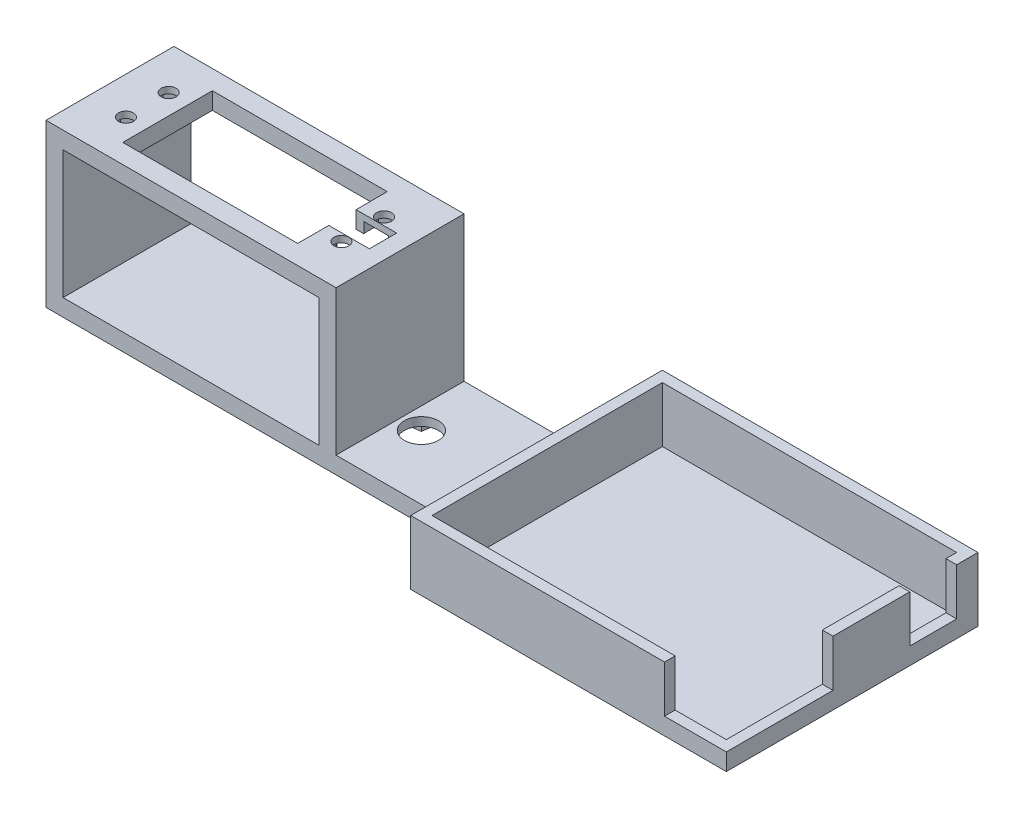
SolidWorks part; units mm, degrees
ref_plane "Front Plane" through (0, 0, 0) normal (0, 0, 1) x (1, 0, 0)
ref_plane "Top Plane" through (0, 0, 0) normal (0, 1, 0) x (1, 0, 0)
ref_plane "Right Plane" through (0, 0, 0) normal (1, 0, 0) x (0, 0, -1)
sketch "Sketch1" plane through (0, 0, 0) normal (0, 1, 0) x (1, 0, 0)
  line L1 (-37, -29.5) -> (37, -29.5)
  line L2 (-37, -29.5) -> (-37, 29.5)
  line L3 (-37, 29.5) -> (37, 29.5)
  line L4 (37, -29.5) -> (37, 29.5)
  line L5 (-37, -29.5) -> (37, 29.5) construction
  line L6 (-37, 29.5) -> (37, -29.5) construction
  point P0 (0, 0)
  dimension "D1" = 59
  dimension "D2" = 74
extrude "Boss-Extrude1" add sketch "Sketch1" along normal blind 2
sketch "Sketch2" plane through (0, 2, 0) normal (0, 1, 0) x (1, 0, 0)
  line L1 (-37, -29.5) -> (37, -29.5)
  line L2 (-37, -29.5) -> (-37, 29.5)
  line L3 (-37, 29.5) -> (37, 29.5)
  line L4 (37, -29.5) -> (37, 29.5)
  line L5 (-37, -29.5) -> (37, 29.5) construction
  line L6 (-37, 29.5) -> (37, -29.5) construction
  line L7 (-34.5, -27) -> (34.5, -27)
  line L8 (-34.5, -27) -> (-34.5, 27)
  line L9 (-34.5, 27) -> (34.5, 27)
  line L10 (34.5, -27) -> (34.5, 27)
  line L11 (-34.5, -27) -> (34.5, 27) construction
  line L12 (-34.5, 27) -> (34.5, -27) construction
  point P0 (0, 0)
  point P7 (0, 0)
  dimension "D1" = 69
  dimension "D2" = 54
extrude "Boss-Extrude2" add sketch "Sketch2" along normal blind 2
sketch "Sketch3" plane through (0, 4, 0) normal (0, 1, 0) x (1, 0, 0)
  line L0 (22.5, -27) -> (22.5, -29.5)
  line L1 (-34.5, -27) -> (34.5, -27) construction
  line L2 (-37, -29.5) -> (37, -29.5) construction
  line L3 (22.5, -29.5) -> (-37, -29.5)
  line L4 (-37, -29.5) -> (-37, 29.5)
  line L5 (-37, 29.5) -> (37, 29.5)
  line L6 (37, 29.5) -> (37, 24.5)
  line L7 (37, -29.5) -> (37, 29.5) construction
  line L8 (37, 24.5) -> (34.5, 24.5)
  line L9 (34.5, -27) -> (34.5, 27) construction
  line L10 (34.5, 24.5) -> (34.5, 27)
  line L11 (34.5, 27) -> (-34.5, 27)
  line L12 (-34.5, 27) -> (-34.5, -27) construction
  line L13 (-34.5, 27) -> (-34.5, -27)
  line L14 (-34.5, -27) -> (22.5, -27)
  line L15 (34.5, 13.5) -> (37, 13.5)
  line L16 (37, 13.5) -> (37, -4.5)
  line L17 (37, -4.5) -> (34.5, -4.5)
  line L18 (34.5, -4.5) -> (34.5, 13.5)
  dimension "D1" = 2.5
  dimension "D2" = 11
  dimension "D3" = 18
  dimension "D4" = 12
extrude "Boss-Extrude3" add sketch "Sketch3" along normal blind 11
sketch "Sketch4" plane through (-37, 0, 0) normal (-1, 0, 0) x (0, 0, 1)
  line L0 (-29.5, 0) -> (29.5, 0) construction
  line L1 (-15, 0) -> (15, 0)
  line L2 (-15, 0) -> (-15, 4)
  line L3 (-15, 4) -> (15, 4)
  line L4 (15, 0) -> (15, 4)
  point P6 (0, 0)
  dimension "D1" = 4
  dimension "D2" = 30
extrude "Boss-Extrude4" add sketch "Sketch4" along normal blind 100
sketch "Sketch5" plane through (0, 4, 0) normal (0, 1, 0) x (1, 0, 0)
  line L0 (-137, -15) -> (-37, -15) construction
  line L1 (-73, 15) -> (-69, 15)
  line L2 (-73, 15) -> (-73, -15)
  line L3 (-73, -15) -> (-69, -15)
  line L4 (-69, 15) -> (-69, -15)
  line L5 (-137, 15) -> (-37, 15) construction
  line L6 (-133, -15) -> (-137, -15)
  line L7 (-133, -15) -> (-133, 15)
  line L8 (-133, 15) -> (-137, 15)
  line L9 (-137, -15) -> (-137, 15)
  line L10 (-137, -15) -> (-137, 15) construction
  dimension "D1" = 4
  dimension "D2" = 60
extrude "Boss-Extrude5" add sketch "Sketch5" along normal blind 30
sketch "Sketch6" plane through (0, 34, 0) normal (0, 1, 0) x (1, 0, 0)
  line L0 (-123.5, 10.5) -> (-82.5, -10.5) construction
  line L1 (-137, 15) -> (-69, 15)
  line L2 (-137, 15) -> (-137, -15)
  line L3 (-137, -15) -> (-69, -15)
  line L4 (-69, 15) -> (-69, -15)
  line L5 (-123.5, 10.5) -> (-82.5, 10.5)
  line L6 (-123.5, 10.5) -> (-123.5, -10.5)
  line L7 (-123.5, -10.5) -> (-82.5, -10.5)
  line L8 (-82.5, 10.5) -> (-82.5, -10.5)
  line L9 (-82.5, 10.5) -> (-123.5, -10.5) construction
  line L10 (-137, -15) -> (-69, 15) construction
  line L11 (-69, -15) -> (-137, 15) construction
  point P10 (-103, 0)
  point P11 (-103, 0)
  dimension "D1" = 41
  dimension "D2" = 21
extrude "Boss-Extrude6" add sketch "Sketch6" along normal blind 4
sketch "Sketch7" plane through (0, 38, 0) normal (0, 1, 0) x (1, 0, 0)
  line L0 (-123.5, 10.5) -> (-123.5, -10.5) construction
  line L2 (-128.25, 5) -> (-77.75, 5) construction
  line L3 (-20.9, 0) -> (20.9, 0) construction
  line L4 (-128.25, -5) -> (-77.75, -5) construction
  line L5 (-123.5, 0) -> (-82.5, 0) construction
  line L6 (-82.5, -10.5) -> (-82.5, 10.5) construction
  line L7 (-103, 0) -> (-103, 10) construction
  line L8 (-73, 15) -> (-73, -15) construction
  line L9 (-82.5, 3.2) -> (-73, 3.2)
  line L10 (-82.5, 3.2) -> (-82.5, -3.2)
  line L11 (-82.5, -3.2) -> (-73, -3.2)
  line L12 (-73, 3.2) -> (-73, -3.2)
  circle A0 centre (-128.25, 5) radius 1.75
  circle A1 centre (-77.75, 5) radius 1.75
  circle A2 centre (-77.75, -5) radius 1.75
  circle A3 centre (-128.25, -5) radius 1.75
  point P8 (-123.5, 0)
  point P19 (-103, 5)
  point P24 (-82.5, 0)
  dimension "D1" = 3.5
  dimension "D2" = 3.5
  dimension "D3" = 50.5
  dimension "D4" = 6.4
  dimension "D5" = 5
extrude "Cut-Extrude1" cut sketch "Sketch7" against normal blind 5
sketch "Sketch8" plane through (0, 34, 0) normal (0, -1, 0) x (1, 0, 0)
  line L1 (-131.25, 6.7321) -> (-131.25, 3.2679)
  line L2 (-131.25, 3.2679) -> (-128.25, 1.5359)
  line L3 (-128.25, 1.5359) -> (-125.25, 3.2679)
  line L4 (-125.25, 3.2679) -> (-125.25, 6.7321)
  line L5 (-125.25, 6.7321) -> (-128.25, 8.4641)
  line L6 (-128.25, 8.4641) -> (-131.25, 6.7321)
  line L7 (-128.25, -1.5359) -> (-131.25, -3.2679)
  line L8 (-131.25, -3.2679) -> (-131.25, -6.7321)
  line L9 (-131.25, -6.7321) -> (-128.25, -8.4641)
  line L10 (-128.25, -8.4641) -> (-125.25, -6.7321)
  line L11 (-125.25, -6.7321) -> (-125.25, -3.2679)
  line L12 (-125.25, -3.2679) -> (-128.25, -1.5359)
  line L13 (-74.75, 3.2679) -> (-74.75, 6.7321)
  line L14 (-74.75, 6.7321) -> (-77.75, 8.4641)
  line L15 (-77.75, 8.4641) -> (-80.75, 6.7321)
  line L16 (-80.75, 6.7321) -> (-80.75, 3.2679)
  line L17 (-80.75, 3.2679) -> (-77.75, 1.5359)
  line L18 (-77.75, 1.5359) -> (-74.75, 3.2679)
  line L19 (-74.75, -6.7321) -> (-74.75, -3.2679)
  line L20 (-74.75, -3.2679) -> (-77.75, -1.5359)
  line L21 (-77.75, -1.5359) -> (-80.75, -3.2679)
  line L22 (-80.75, -3.2679) -> (-80.75, -6.7321)
  line L23 (-80.75, -6.7321) -> (-77.75, -8.4641)
  line L24 (-77.75, -8.4641) -> (-74.75, -6.7321)
  circle A0 centre (-128.25, 5) radius 3 construction
  circle A1 centre (-128.25, -5) radius 3 construction
  circle A2 centre (-77.75, 5) radius 3 construction
  circle A3 centre (-77.75, -5) radius 3 construction
  dimension "D1" = 6
  dimension "D2" = 6
  dimension "D3" = 6
  dimension "D4" = 6
extrude "Cut-Extrude2" cut sketch "Sketch8" against normal blind 2.5
sketch "Sketch9" plane through (0, 4, 0) normal (0, 1, 0) x (1, 0, 0)
  line L0 (-69, -15) -> (-69, 15) construction
  circle A0 centre (-64, 0) radius 4
  dimension "D1" = 8
  dimension "D2" = 5
extrude "Cut-Extrude3" cut sketch "Sketch9" against normal blind 10
sketch "Sketch10" plane through (0, 0, 0) normal (0, -1, 0) x (1, 0, 0)
  circle A0 centre (-64, 0) radius 4 construction
  ellipse E0 centre (-64, 0) end of major axis (-64, 12.5) minor radius 4
  ellipse E1 centre (-64, 0) end of major axis (-51.5, 0) minor radius 4
  point P1 (-60, 0)
  point P15 (-64, 4)
  dimension "D1" = 25
  dimension "D2" = 25
extrude "Cut-Extrude4" cut sketch "Sketch10" against normal blind 2
